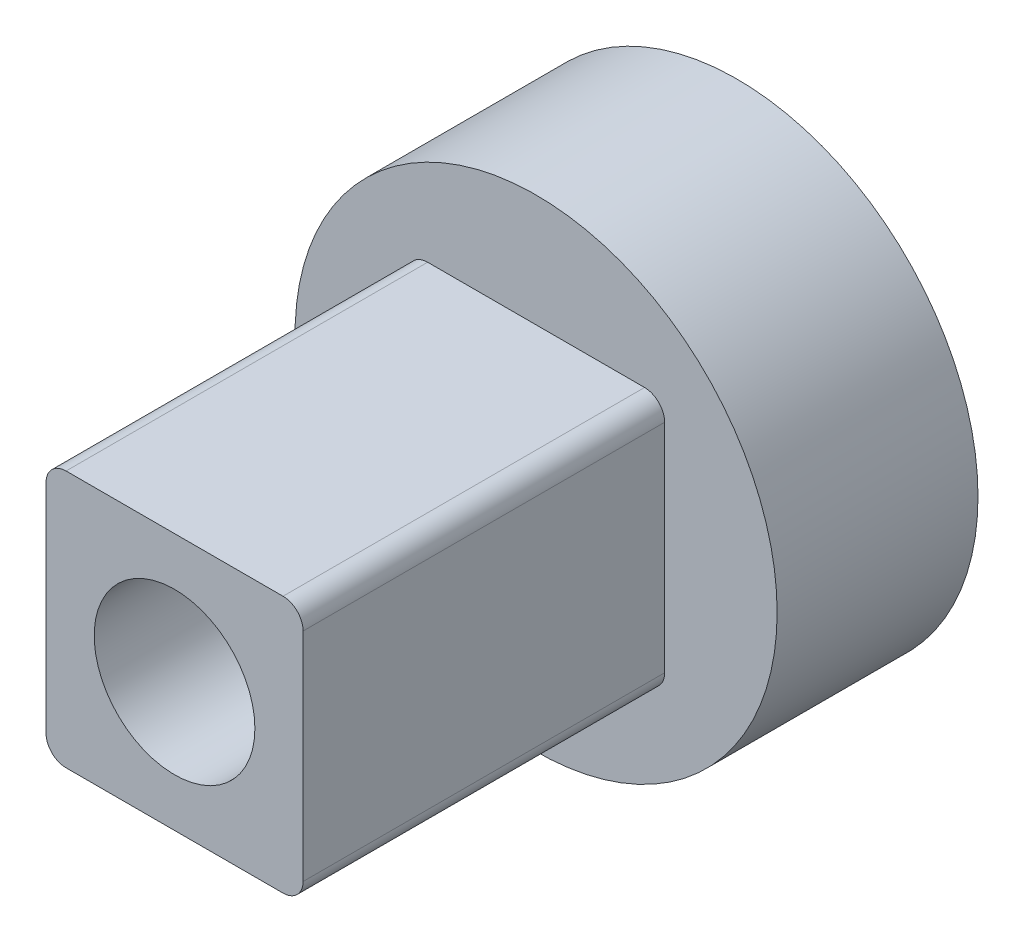
SolidWorks part; units mm, degrees
ref_plane "Front Plane" through (0, 0, 0) normal (0, 0, 1) x (1, 0, 0)
ref_plane "Top Plane" through (0, 0, 0) normal (0, 1, 0) x (1, 0, 0)
ref_plane "Right Plane" through (0, 0, 0) normal (1, 0, 0) x (0, 0, -1)
sketch "Sketch1" plane through (0, 0, -23.4655) normal (0, 0, 1) x (1, 0, 0)
  circle A0 centre (3.7405, -31.8284) radius 2.4
  circle A1 centre (3.7405, -31.8284) radius 6
  dimension "D1" = 4.8
  dimension "D2" = 12
extrude "Boss-Extrude1" add sketch "Sketch1" along normal blind 5
sketch "Sketch2" plane through (0, 0, -18.4655) normal (0, 0, 1) x (1, 0, 0)
  line L4 (3.7405, -31.8284) -> (6.9405, -31.8284) construction
  line L5 (6.9405, -31.8284) -> (6.9405, -28.6284) construction
  line L7 (6.4405, -28.6284) -> (1.0405, -28.6284)
  line L8 (6.9405, -29.1284) -> (6.9405, -34.5284)
  line L9 (6.4405, -35.0284) -> (1.0405, -35.0284)
  line L10 (0.5405, -29.1284) -> (0.5405, -34.5284)
  arc A1 (0.5405, -29.1284) -> (1.0405, -28.6284) centre (1.0405, -29.1284) cw
  arc A2 (1.0405, -35.0284) -> (0.5405, -34.5284) centre (1.0405, -34.5284) cw
  arc A3 (6.4405, -35.0284) -> (6.9405, -34.5284) centre (6.4405, -34.5284) ccw
  arc A4 (6.4405, -28.6284) -> (6.9405, -29.1284) centre (6.4405, -29.1284) cw
  point P6 (0.5405, -28.6284)
  point P12 (0.5405, -35.0284)
  point P15 (6.9405, -35.0284)
  dimension "D5" = 0.5
  dimension "D6" = 0.5
  dimension "D1" = 3.2
  dimension "D2" = 3.2
  dimension "D3" = 6.4
  dimension "D4" = 6.4
extrude "Boss-Extrude2" add sketch "Sketch2" along normal blind 9
sketch "Sketch3" plane through (0, 0, -9.4655) normal (0, 0, 1) x (1, 0, 0)
  circle A0 centre (3.7405, -31.8284) radius 1
  dimension "D1" = 2
extrude "Cut-Extrude1" cut sketch "Sketch3" against normal up to next
sketch "Sketch4" plane through (0, 0, -9.4655) normal (0, 0, 1) x (1, 0, 0)
  circle A0 centre (3.7405, -31.8284) radius 2
  dimension "D1" = 4
extrude "Cut-Extrude2" cut sketch "Sketch4" against normal offset from surface (7 mm away) 2 up to face at (9.7405, -31.8284, -18.4655)
